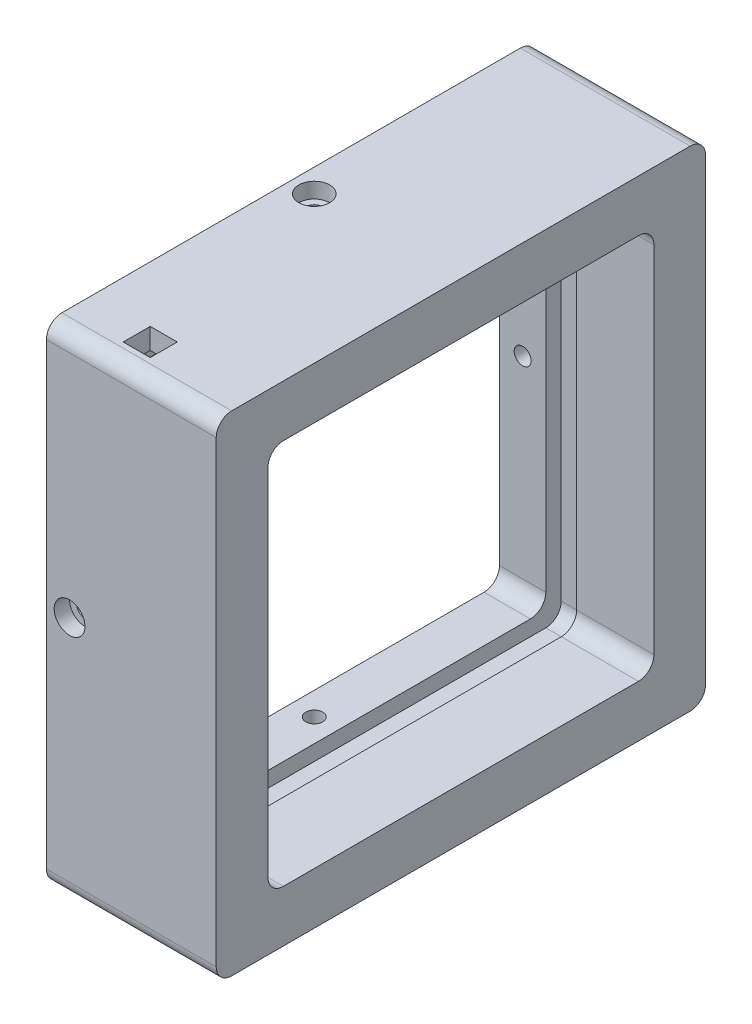
SolidWorks part; units mm, degrees
ref_plane "前视基准面" through (0, 0, 0) normal (0, 0, 1) x (1, 0, 0)
ref_plane "上视基准面" through (0, 0, 0) normal (0, 1, 0) x (1, 0, 0)
ref_plane "右视基准面" through (0, 0, 0) normal (1, 0, 0) x (0, 0, -1)
sketch "草图1" plane through (0, 0, 0) normal (1, 0, 0) x (0, 0, -1)
  line L1 (-31.7, 31.7) -> (31.7, 31.7)
  line L2 (-31.7, 31.7) -> (-31.7, -31.7)
  line L3 (-31.7, -31.7) -> (31.7, -31.7)
  line L4 (31.7, 31.7) -> (31.7, -31.7)
  line L5 (-31.7, 31.7) -> (31.7, -31.7) construction
  line L6 (-31.7, -31.7) -> (31.7, 31.7) construction
  point P0 (0, 0)
extrude "凸台-拉伸1" add sketch "草图1" along normal blind 22
sketch "草图2" plane through (22, 0, 0) normal (1, 0, 0) x (0, 0, -1)
  line L1 (-25, 25) -> (25, 25)
  line L2 (-25, 25) -> (-25, -25)
  line L3 (-25, -25) -> (25, -25)
  line L4 (25, 25) -> (25, -25)
  line L5 (-25, 25) -> (25, -25) construction
  line L6 (-25, -25) -> (25, 25) construction
  point P0 (0, 0)
extrude "切除-拉伸1" cut sketch "草图2" against normal blind 10
sketch "草图3" plane through (0, 0, 0) normal (-1, 0, 0) x (0, 0, 1)
  line L1 (-27, 27) -> (27, 27)
  line L2 (-27, 27) -> (-27, -27)
  line L3 (-27, -27) -> (27, -27)
  line L4 (27, 27) -> (27, -27)
  line L5 (-27, 27) -> (27, -27) construction
  line L6 (-27, -27) -> (27, 27) construction
  point P0 (0, 0)
extrude "切除-拉伸2" cut sketch "草图3" against normal blind 12
sketch "草图4" plane through (0, 27, 0) normal (0, -1, 0) x (-1, 0, 0)
  line L0 (-12, -27) -> (0, -27) construction
  line L1 (-12, 27) -> (-6, 27)
  line L2 (-12, 27) -> (-12, -27)
  line L3 (-12, -27) -> (-6, -27)
  line L4 (-6, 27) -> (-6, -27)
extrude "切除-拉伸3" cut sketch "草图4" against normal blind 2
sketch "草图5" plane through (0, 0, -27) normal (0, 0, 1) x (1, 0, 0)
  line L0 (12, -27) -> (0, -27) construction
  line L1 (12, 29) -> (6, 29)
  line L2 (12, 29) -> (12, -27)
  line L3 (12, -27) -> (6, -27)
  line L4 (6, 29) -> (6, -27)
extrude "切除-拉伸4" cut sketch "草图5" against normal blind 2
sketch "草图6" plane through (0, -27, 0) normal (0, 1, 0) x (1, 0, 0)
  line L0 (12, -27) -> (0, -27) construction
  line L1 (12, 29) -> (6, 29)
  line L2 (12, 29) -> (12, -27)
  line L3 (12, -27) -> (6, -27)
  line L4 (6, 29) -> (6, -27)
extrude "切除-拉伸5" cut sketch "草图6" against normal blind 2
sketch "草图8" plane through (0, 0, 27) normal (0, 0, -1) x (-1, 0, 0)
  line L0 (-6, -29) -> (-12, -29) construction
  line L1 (-12, 29) -> (-6, 29)
  line L2 (-12, 29) -> (-12, -29)
  line L3 (-12, -29) -> (-6, -29)
  line L4 (-6, 29) -> (-6, -29)
extrude "切除-拉伸9" cut sketch "草图8" against normal blind 2
sketch "草图9" plane through (0, 29, 0) normal (0, -1, 0) x (-1, 0, 0)
  line L3 (-7.25, -29) -> (-10.75, -29)
  line L4 (-7.25, -29) -> (-7.25, -25.5)
  line L5 (-7.25, -25.5) -> (-10.75, -25.5)
  line L6 (-10.75, -29) -> (-10.75, -25.5)
  line L7 (-7.25, -29) -> (-10.75, -25.5) construction
  line L8 (-7.25, -25.5) -> (-10.75, -29) construction
extrude "切除-拉伸11" cut sketch "草图9" against normal up to next
sketch "草图10" plane through (0, 0, -31.7) normal (0, 0, -1) x (-1, 0, 0)
  circle A0 centre (-3, 0) radius 2
extrude "切除-拉伸12" cut sketch "草图10" against normal blind 2
sketch "草图11" plane through (0, 0, -29.7) normal (0, 0, -1) x (-1, 0, 0)
  circle A0 centre (-3, 0) radius 1.1
extrude "切除-拉伸13" cut sketch "草图11" against normal up to next contours A0
sketch "草图12" plane through (0, 0, 31.7) normal (0, 0, 1) x (1, 0, 0)
  circle A0 centre (3, 0) radius 2
extrude "切除-拉伸14" cut sketch "草图12" against normal blind 2
sketch "草图13" plane through (0, 0, 31.7) normal (0, 0, 1) x (1, 0, 0)
  circle A0 centre (3, 0) radius 1.1
extrude "切除-拉伸15" cut sketch "草图13" against normal up to next
sketch "草图14" plane through (0, -31.7, 0) normal (0, -1, 0) x (-1, 0, 0)
  circle A0 centre (-3, 0) radius 2
extrude "切除-拉伸16" cut sketch "草图14" against normal blind 2
sketch "草图15" plane through (0, -29.7, 0) normal (0, -1, 0) x (-1, 0, 0)
  circle A0 centre (-3, 0) radius 1.1
extrude "切除-拉伸17" cut sketch "草图15" against normal up to next
sketch "草图16" plane through (0, 31.7, 0) normal (0, 1, 0) x (1, 0, 0)
  circle A0 centre (3, 0) radius 2
extrude "切除-拉伸18" cut sketch "草图16" against normal blind 2
sketch "草图17" plane through (0, 29.7, 0) normal (0, 1, 0) x (1, 0, 0)
  circle A0 centre (3, 0) radius 1.1
extrude "切除-拉伸19" cut sketch "草图17" against normal up to next
fillet "圆角1" radius 2 3 edges at (9, 29, -29) (9, -29, -29) (9, -29, 29)
fillet "圆角2" radius 2 4 edges at (17, -25, 25) (17, 25, 25) (17, 25, -25) (17, -25, -25)
fillet "圆角3" radius 2 4 edges at (3, -27, 27) (3, -27, -27) (3, 27, -27) (3, 27, 27)
fillet "圆角4" radius 2 4 edges at (11, 31.7, 31.7) (11, 31.7, -31.7) (11, -31.7, 31.7) (11, -31.7, -31.7)
